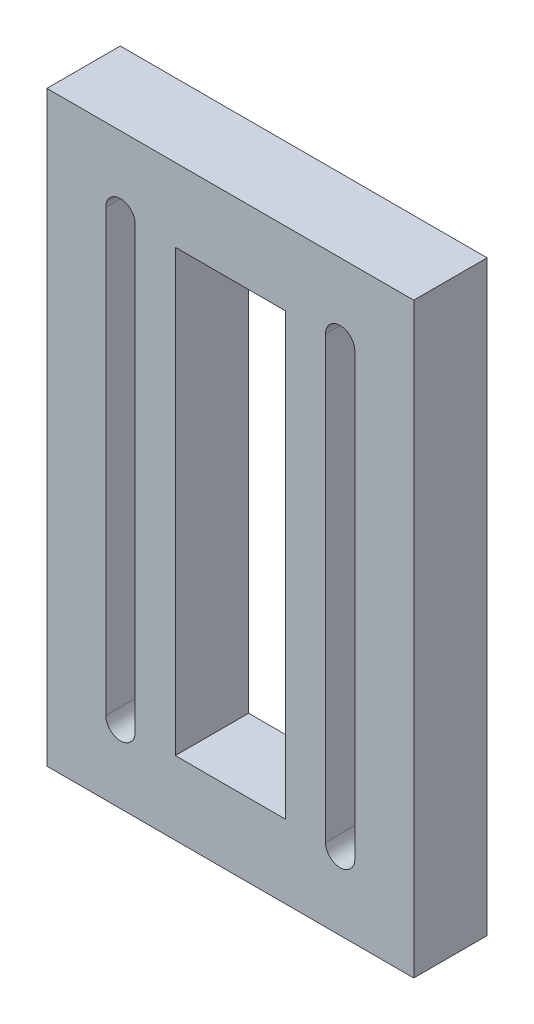
SolidWorks part; units mm, degrees
material "Pin"
ref_plane "Plan de face" through (0, 0, 0) normal (0, 0, 1) x (1, 0, 0)
ref_plane "Plan de dessus" through (0, 0, 0) normal (0, 1, 0) x (1, 0, 0)
ref_plane "Plan de droite" through (0, 0, 0) normal (1, 0, 0) x (0, 0, -1)
sketch "Esquisse1" plane through (0, 0, 0) normal (0, 0, 1) x (1, 0, 0)
  line L0 (-21.9353, 0) -> (-11.9041, 0) construction
  line L1 (-21.9353, 40) -> (28.0647, 40)
  line L2 (-21.9353, 40) -> (-21.9353, -40)
  line L3 (-21.9353, -40) -> (28.0647, -40)
  line L4 (28.0647, 40) -> (28.0647, -40)
  line L5 (-11.9041, 0) -> (-4.4353, 0) construction
  line L6 (18.0335, 0) -> (28.0647, 0) construction
  line L7 (-11.9041, 40) -> (-11.9041, 30) construction
  line L8 (-11.9041, 30) -> (-11.9041, 0) construction
  line L9 (-11.9041, 0) -> (-11.9041, -30) construction
  line L10 (-11.9041, -30) -> (-11.9041, -40) construction
  line L11 (18.0335, 40) -> (18.0335, 30) construction
  line L12 (18.0335, 30) -> (18.0335, 0) construction
  line L13 (18.0335, 0) -> (18.0335, -30) construction
  line L14 (18.0335, -30) -> (18.0335, -40) construction
  line L15 (-13.9041, 30) -> (-13.9041, -30)
  line L16 (-9.9041, 30) -> (-9.9041, -30)
  line L17 (16.0335, 30) -> (16.0335, -30)
  line L18 (20.0335, -30) -> (20.0335, 30)
  line L19 (-4.4353, 0) -> (10.5647, 0) construction
  line L20 (10.5647, 0) -> (18.0335, 0) construction
  line L21 (-4.4353, 0) -> (-4.4353, 30)
  line L22 (-4.4353, 30) -> (10.5647, 30)
  line L23 (10.5647, 30) -> (10.5647, 0)
  line L24 (10.5647, 0) -> (10.5647, -30)
  line L25 (10.5647, -30) -> (-4.4353, -30)
  line L26 (-4.4353, -30) -> (-4.4353, 0)
  arc A0 (-13.9041, 30) -> (-9.9041, 30) centre (-11.9041, 30) cw
  arc A1 (-13.9041, -30) -> (-9.9041, -30) centre (-11.9041, -30) ccw
  arc A2 (16.0335, 30) -> (20.0335, 30) centre (18.0335, 30) cw
  arc A3 (20.0335, -30) -> (16.0335, -30) centre (18.0335, -30) cw
  dimension "D2" = 2
  dimension "D1" = 50
  dimension "D3" = 60
  dimension "D4" = 80
  dimension "D5" = 15
  dimension "D6" = 10
extrude "Boss.-Extru.1" add sketch "Esquisse1" along normal blind 10
